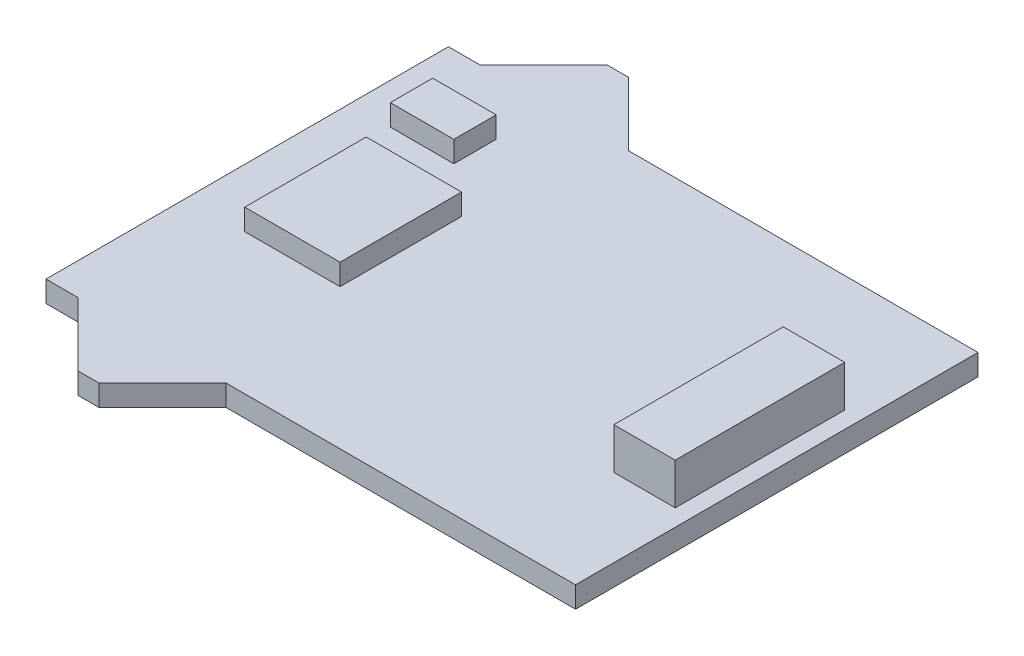
SolidWorks part; units mm, degrees
ref_plane "Front Plane" through (0, 0, 0) normal (0, 0, 1) x (1, 0, 0)
ref_plane "Top Plane" through (0, 0, 0) normal (0, 1, 0) x (1, 0, 0)
ref_plane "Right Plane" through (0, 0, 0) normal (1, 0, 0) x (0, 0, -1)
sketch "Sketch1" plane through (0, 0, 0) normal (0, 1, 0) x (1, 0, 0)
  line L0 (-3.5, 9.5) -> (-0.5, 12.5)
  line L1 (-5, -9.5) -> (5, -9.5) construction
  line L2 (-5, -9.5) -> (-5, 9.5) construction
  line L3 (-5, 9.5) -> (-3.5, 9.5)
  line L4 (5, -9.5) -> (5, 9.5) construction
  line L5 (-5, -9.5) -> (5, 9.5) construction
  line L6 (-5, 9.5) -> (5, -9.5) construction
  line L7 (-0.5, 12.5) -> (0.5, 12.5)
  line L8 (0.5, 12.5) -> (3.5, 9.5)
  line L9 (3.5, 9.5) -> (5, 9.5)
  line L10 (-5, 0) -> (5, 0) construction
  line L11 (3.5, -9.5) -> (5, -9.5)
  line L12 (5, 9.5) -> (20, 9.5)
  line L13 (5, 9.5) -> (5, -9.5) construction
  line L14 (5, -9.5) -> (20, -9.5)
  line L15 (20, 9.5) -> (20, -9.5)
  line L16 (0.5, -12.5) -> (3.5, -9.5)
  line L17 (-0.5, -12.5) -> (0.5, -12.5)
  line L18 (-5, -9.5) -> (-3.5, -9.5)
  line L19 (-3.5, -9.5) -> (-0.5, -12.5)
  line L20 (-5, 9.5) -> (-5, -9.5)
  point P0 (0, 0)
  point P8 (0, 12.5)
  dimension "D1" = 19
  dimension "D2" = 3
  dimension "D3" = 5
  dimension "D4" = 7
  dimension "D5" = 25
extrude "Boss-Extrude1" add sketch "Sketch1" against normal blind 1
sketch "Sketch2" plane through (0, 0, 0) normal (0, 1, 0) x (1, 0, 0)
  line L1 (-2.25, -2.8676) -> (2.25, -2.8676)
  line L2 (-2.25, -2.8676) -> (-2.25, 2.8676)
  line L3 (-2.25, 2.8676) -> (2.25, 2.8676)
  line L4 (2.25, -2.8676) -> (2.25, 2.8676)
  line L5 (-2.25, -2.8676) -> (2.25, 2.8676) construction
  line L6 (-2.25, 2.8676) -> (2.25, -2.8676) construction
  line L7 (-3.0875, 4.842) -> (-0.0875, 4.842)
  line L8 (-3.0875, 4.842) -> (-3.0875, 6.842)
  line L9 (-3.0875, 6.842) -> (-0.0875, 6.842)
  line L10 (-0.0875, 4.842) -> (-0.0875, 6.842)
  line L11 (-3.0875, 4.842) -> (-0.0875, 6.842) construction
  line L12 (-3.0875, 6.842) -> (-0.0875, 4.842) construction
  point P0 (0, 0)
  point P6 (-1.5875, 5.842)
  dimension "D1" = 5.7352
  dimension "D2" = 4.5
  dimension "D3" = 3
  dimension "D4" = 2
  dimension "D5" = 5.842
  dimension "D6" = 1.5875
extrude "Boss-Extrude2" add sketch "Sketch2" along normal blind 1
sketch "Sketch3" plane through (0, 0, 0) normal (0, 1, 0) x (1, 0, 0)
  line L0 (20, -9.5) -> (20, 9.5) construction
  line L6 (16.3063, -4) -> (16.3063, 4)
  line L8 (16.3063, -4) -> (19.2063, -4)
  line L9 (19.2063, -4) -> (19.2063, 4)
  line L10 (16.3063, 4) -> (19.2063, 4)
  point P4 (20.254, -4)
  point P5 (19.2001, -4)
  point P8 (16.3063, 0)
  dimension "D1" = 8
  dimension "D2" = 2.9
  dimension "D3" = 0.7937
extrude "Boss-Extrude3" add sketch "Sketch3" along normal blind 1.95
sketch "Sketch4" plane through (0, 0, 0) normal (0, 1, 0) x (1, 0, 0)
  line L1 (17.8272, 3.99) -> (21.3134, 3.99)
  line L2 (17.8272, 3.99) -> (17.8272, -4.5386)
  line L3 (17.8272, -4.5386) -> (21.3134, -4.5386)
  line L4 (21.3134, 3.99) -> (21.3134, -4.5386)
extrude "Boss-Extrude4" [suppressed] add sketch "Sketch4" along normal blind 3
equation "\"width\"= 19mm"
equation "\"D1@Sketch1\"=\"width\""
equation "\"encoder_side_offse\"= 5mm"
equation "\"D3@Sketch1\"=\"encoder_side_offse\""
equation "\"nub_height\"= 3mm"
equation "\"D2@Sketch1\"=\"nub_height\""
equation "\"nub_width\"= 7mm"
equation "\"D4@Sketch1\"=\"nub_width\""
equation "\"pcb_length\"= 25mm"
equation "\"pcb_thickness\"= 1mm"
equation "\"D1@Boss-Extrude1\"=\"pcb_thickness\""
equation "\"encoder_width\"= 6mm"
equation "\"encoder_length\"= 4.5mm"
equation "\"D2@Sketch2\"=\"encoder_length\""
equation "\"plugin_side_offset\"= 1.5mm"
equation "\"connector_length\"= 2.9mm"
equation "\"D5@Sketch1\"=\"pcb_length\""
equation "\"connector_height\"= 1.95mm"
equation "\"connector_width\"= 8mm"
equation "\"D1@Sketch3\"=\"connector_width\""
equation "\"D1@Boss-Extrude3\"=\"connector_height\""
equation "\"D2@Sketch3\"=\"connector_length\""
